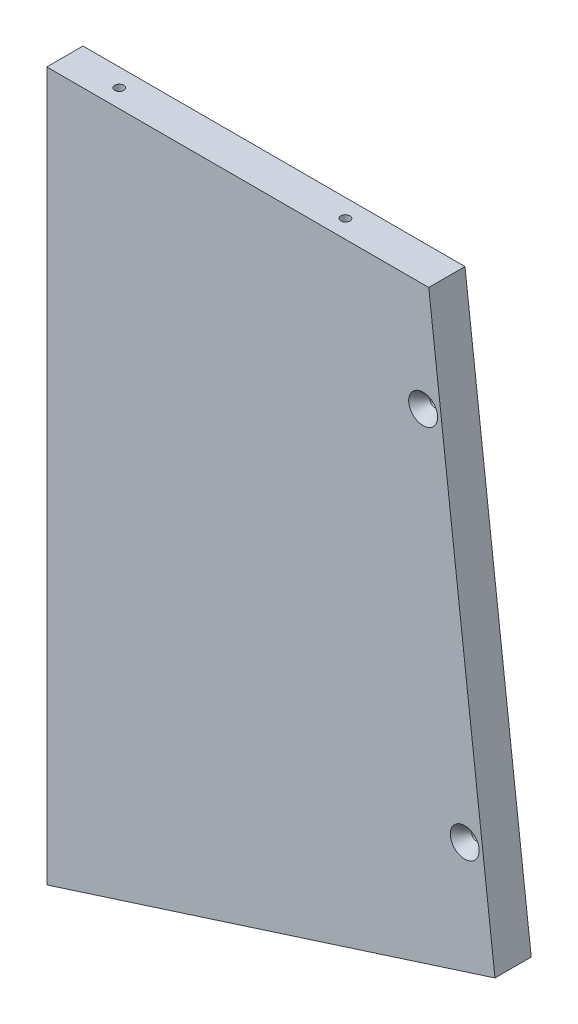
SolidWorks part; units mm, degrees
material "Beech"
ref_plane "Front Plane" through (0, 0, 0) normal (0, 0, 1) x (1, 0, 0)
ref_plane "Top Plane" through (0, 0, 0) normal (0, 1, 0) x (1, 0, 0)
ref_plane "Right Plane" through (0, 0, 0) normal (1, 0, 0) x (0, 0, -1)
sketch "Sketch1" plane through (0, 0, 0) normal (0, 0, 1) x (1, 0, 0)
  line L1 (-222.053, -248.25) -> (-222.053, 0) construction
  line L2 (-88.1902, 0) -> (-222.053, 0)
  line L3 (-222.053, -248.25) -> (-222.053, 0)
  line L4 (-91.9973, 0) -> (-234.753, 0) construction
  line L7 (-64.9774, -197.966) -> (-88.1902, 0)
  line L8 (-64.9774, -197.966) -> (-222.053, -248.25)
extrude "Boss-Extrude1" add sketch "Sketch1" against normal blind 12.7
hole_wizard "Hole1" positions "Sketch2" profile "Sketch3" legacy
sketch "Sketch2" plane through (181.0394, 12.7, 123.1167) normal (0, 1, 0) x (0, 0, -1)
  line L0 (-129.4667, 415.7924) -> (-129.4667, 273.0368) construction
  line L5 (-135.8167, 409.4424) -> (135.5488, 409.4424) construction
  line L10 (-135.8167, 279.3868) -> (135.5488, 279.3868) construction
  line L11 (-0.134, 409.4424) -> (-0.134, 279.3868) construction
  point P22 (-129.4667, 384.0424)
  point P24 (-129.4667, 304.7868)
  point P26 (-110.4167, 409.4424)
  point P30 (-0.134, 409.4424)
  point P50 (110.1488, 409.4424)
  point P51 (129.1988, 304.7868)
  point P52 (129.1988, 384.0424)
sketch "Sketch3" plane through (-203.003, 12.7, -6.082) normal (1, 0, 0) x (0, 0, 1)
  line L0 (0, 0) -> (0, 32.7039)
  line L1 (0, 32.7039) -> (1.5875, 31.75)
  line L2 (1.5875, 31.75) -> (1.5875, 4.0177)
  line L3 (1.5875, 4.0177) -> (5.08, 0)
  line L4 (5.08, 0) -> (0, 0)
  line L5 (0, -14.3089) -> (0, 102.4216) construction
  line L6 (0, 32.7039) -> (-1.5875, 31.75) construction
  line L7 (-1.5875, 4.0177) -> (-5.08, 0) construction
  dimension "Diameter" = 3.175
  dimension "Depth" = 31.75
  dimension "C-Sink Diameter" = 10.16
  dimension "C-Sink Angle" = 82
  dimension "Drill Angle" = 118
hole_wizard "Hole3" positions "Sketch6" profile "Sketch7" legacy
sketch "Sketch6" plane through (-234.753, 1090.5128, -135.8167) normal (-1, 0, 0) x (0, 0, -1)
  line L3 (-0.134, 1338.7628) -> (-0.134, 1090.5128) construction
  point P1 (-129.4667, 1300.6628)
  point P3 (-129.4667, 1128.6128)
  point P15 (129.1988, 1128.6128)
  point P16 (129.1988, 1300.6628)
sketch "Sketch7" plane through (-234.753, -210.15, -6.35) normal (0, 1, 0) x (0, 0, 1)
  line L0 (0, 0) -> (0, 32.7039)
  line L1 (0, 32.7039) -> (1.5875, 31.75)
  line L2 (1.5875, 31.75) -> (1.5875, 4.0177)
  line L3 (1.5875, 4.0177) -> (5.08, 0)
  line L4 (5.08, 0) -> (0, 0)
  line L5 (0, -14.3089) -> (0, 102.4216) construction
  line L6 (0, 32.7039) -> (-1.5875, 31.75) construction
  line L7 (-1.5875, 4.0177) -> (-5.08, 0) construction
  dimension "Diameter" = 3.175
  dimension "Depth" = 31.75
  dimension "C-Sink Diameter" = 10.16
  dimension "C-Sink Angle" = 82
  dimension "Drill Angle" = 118
hole_wizard "Hole5" positions "Sketch10" profile "Sketch11" legacy
sketch "Sketch10" plane through (-234.753, 1090.5128, 123.1167) normal (-1, 0, 0) x (0, 0, -1)
  line L3 (-0.134, 1338.7628) -> (-0.134, 1090.5128) construction
  point P1 (-129.4667, 1300.6628)
  point P3 (-129.4667, 1128.6128)
  point P15 (129.1988, 1128.6128)
  point P16 (129.1988, 1300.6628)
sketch "Sketch11" plane through (-234.753, -210.15, 252.5835) normal (0, 1, 0) x (0, 0, 1)
  line L0 (0, 0) -> (0, 32.7039)
  line L1 (0, 32.7039) -> (1.5875, 31.75)
  line L2 (1.5875, 31.75) -> (1.5875, 4.0177)
  line L3 (1.5875, 4.0177) -> (5.08, 0)
  line L4 (5.08, 0) -> (0, 0)
  line L5 (0, -14.3089) -> (0, 102.4216) construction
  line L6 (0, 32.7039) -> (-1.5875, 31.75) construction
  line L7 (-1.5875, 4.0177) -> (-5.08, 0) construction
  dimension "Diameter" = 3.175
  dimension "Depth" = 31.75
  dimension "C-Sink Diameter" = 10.16
  dimension "C-Sink Angle" = 82
  dimension "Drill Angle" = 118
hole_wizard "Hole6" positions "Sketch12" profile "Sketch13" legacy
sketch "Sketch12" plane through (181.0394, 1090.5128, 0) normal (0, 0, 1) x (-0.9272, -0.3746, 0)
  point P29 (707.1666, 1065.2704)
  point P31 (674.128, 944.6031)
sketch "Sketch13" plane through (-75.5767, -162.098, 0) normal (1, 0, 0) x (0, -1, 0)
  line L0 (0, 0) -> (0, 39.0539)
  line L1 (0, 39.0539) -> (1.5875, 38.1)
  line L2 (1.5875, 38.1) -> (1.5875, 4.0177)
  line L3 (1.5875, 4.0177) -> (5.08, 0)
  line L4 (5.08, 0) -> (0, 0)
  line L5 (0, -14.3089) -> (0, 102.4216) construction
  line L6 (0, 39.0539) -> (-1.5875, 38.1) construction
  line L7 (-1.5875, 4.0177) -> (-5.08, 0) construction
  dimension "Diameter" = 3.175
  dimension "Depth" = 38.1
  dimension "C-Sink Diameter" = 10.16
  dimension "C-Sink Angle" = 82
  dimension "Drill Angle" = 118
hole_wizard "Hole7" positions "Sketch14" profile "Sketch15" legacy
sketch "Sketch14" plane through (181.0394, 12.7, -135.8167) normal (0, 1, 0) x (0, 0, -1)
  line L0 (-129.4667, 415.7924) -> (-129.4667, 273.0368) construction
  line L5 (-135.8167, 409.4424) -> (135.5488, 409.4424) construction
  line L10 (-135.8167, 279.3868) -> (135.5488, 279.3868) construction
  line L11 (-0.134, 409.4424) -> (-0.134, 279.3868) construction
  point P22 (-129.4667, 384.0424)
  point P24 (-129.4667, 304.7868)
  point P26 (-110.4167, 409.4424)
  point P30 (-0.134, 409.4424)
  point P50 (110.1488, 409.4424)
  point P51 (129.1988, 304.7868)
  point P52 (129.1988, 384.0424)
sketch "Sketch15" plane through (-203.003, 12.7, -265.0155) normal (1, 0, 0) x (0, 0, 1)
  line L0 (0, 0) -> (0, 32.7039)
  line L1 (0, 32.7039) -> (1.5875, 31.75)
  line L2 (1.5875, 31.75) -> (1.5875, 4.0177)
  line L3 (1.5875, 4.0177) -> (5.08, 0)
  line L4 (5.08, 0) -> (0, 0)
  line L5 (0, -14.3089) -> (0, 102.4216) construction
  line L6 (0, 32.7039) -> (-1.5875, 31.75) construction
  line L7 (-1.5875, 4.0177) -> (-5.08, 0) construction
  dimension "Diameter" = 3.175
  dimension "Depth" = 31.75
  dimension "C-Sink Diameter" = 10.16
  dimension "C-Sink Angle" = 82
  dimension "Drill Angle" = 118
hole_wizard "Hole8" positions "Sketch16" profile "Sketch17" legacy
sketch "Sketch16" plane through (536.1771, -18.8558, -135.8167) normal (0.3049, -0.9524, 0) x (0, 0, 1)
  line L0 (129.4667, 804.1643) -> (129.4667, 630.143) construction
  line L5 (0.134, 804.1643) -> (0, 630.3901) construction
  point P10 (129.4667, 668.243)
  point P12 (129.4667, 766.0643)
  point P20 (-129.4082, 668.4425)
  point P21 (-129.2574, 766.2637)
sketch "Sketch17" plane through (-193.6044, -252.4777, -265.0741) normal (0, 0, 1) x (0.9524, 0.3049, 0)
  line L0 (0, 0) -> (0, 32.7039)
  line L1 (0, 32.7039) -> (1.5875, 31.75)
  line L2 (1.5875, 31.75) -> (1.5875, 4.0177)
  line L3 (1.5875, 4.0177) -> (5.08, 0)
  line L4 (5.08, 0) -> (0, 0)
  line L5 (0, -14.3089) -> (0, 102.4216) construction
  line L6 (0, 32.7039) -> (-1.5875, 31.75) construction
  line L7 (-1.5875, 4.0177) -> (-5.08, 0) construction
  dimension "Diameter" = 3.175
  dimension "Depth" = 31.75
  dimension "C-Sink Diameter" = 10.16
  dimension "C-Sink Angle" = 82
  dimension "Drill Angle" = 118
